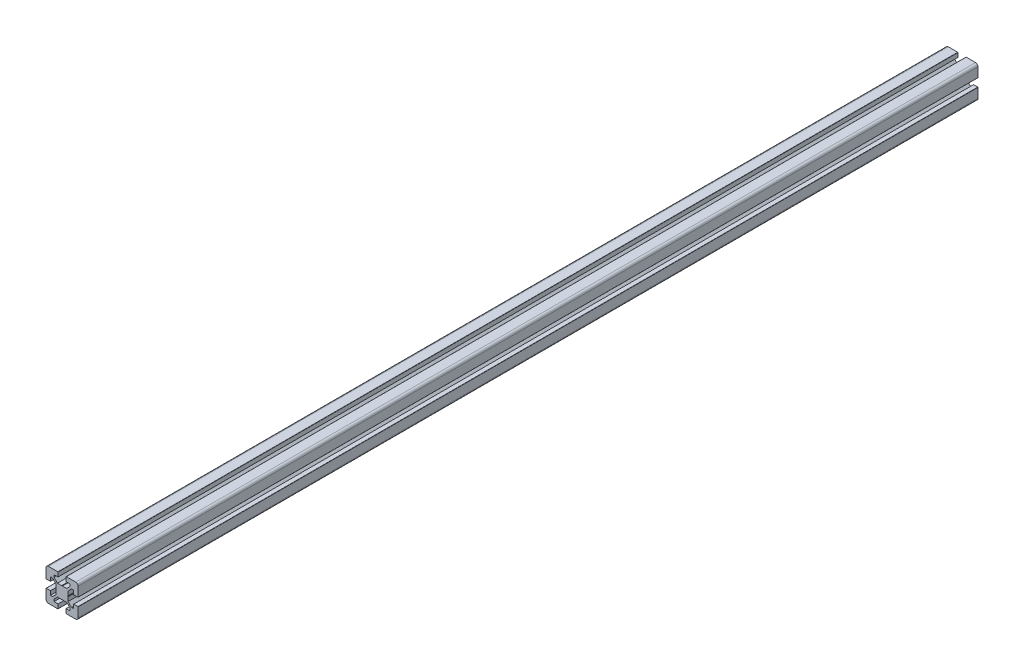
SolidWorks part; units mm, degrees
ref_plane "正面" through (0, 0, 0) normal (0, 0, 1) x (1, 0, 0)
ref_plane "平面" through (0, 0, 0) normal (0, 1, 0) x (1, 0, 0)
ref_plane "右側面" through (0, 0, 0) normal (1, 0, 0) x (0, 0, -1)
sketch "Model" plane through (0, 0, 0) normal (0, 0, 1) x (1, 0, 0)
  line L0 (160, 30) -> (160, 70)
  line L1 (110, 70) -> (110, 30)
  line L2 (160, 30) -> (110, 30)
  line L3 (110, 55) -> (160, 55)
  line L4 (110, 45) -> (160, 45)
  line L5 (160, 70) -> (110, 70)
  line L6 (105, 50) -> (165, 50) construction
  line L7 (110, 50.5196) -> (160, 50.5196)
  line L8 (110, 49.4804) -> (160, 49.4804)
  line L9 (110, 60) -> (160, 60) construction
  line L10 (110, 40) -> (160, 40) construction
  line L11 (37, 68) -> (33, 68)
  line L12 (69.7, 55) -> (64.5, 55)
  line L13 (64.5, 60) -> (64.5, 55)
  line L14 (70, 67) -> (70, 55.3)
  line L15 (68, 67) -> (68, 63)
  line L16 (64.5, 40) -> (64.5, 45)
  line L17 (69.7, 45) -> (64.5, 45)
  line L18 (70, 33) -> (70, 44.7)
  line L19 (68, 33) -> (68, 37)
  line L20 (33, 70) -> (44.7, 70)
  line L21 (60, 64.5) -> (60, 61.7678)
  line L22 (60, 64.5) -> (55, 64.5)
  line L23 (60, 61.7678) -> (55.7322, 57.5)
  line L24 (61.7678, 60) -> (57.5, 55.7322)
  line L25 (40, 64.5) -> (40, 61.7678)
  line L26 (40, 64.5) -> (45, 64.5)
  line L27 (40, 61.7678) -> (44.2678, 57.5)
  line L28 (35.5, 60) -> (38.2322, 60)
  line L29 (30.3, 55) -> (35.5, 55)
  line L30 (38.2322, 60) -> (42.5, 55.7322)
  line L31 (35.5, 55) -> (35.5, 60)
  line L32 (30, 67) -> (30, 55.3)
  line L33 (32, 67) -> (32, 63)
  line L34 (38, 67) -> (38, 63)
  line L35 (45, 69.7) -> (45, 64.5)
  line L36 (55, 69.7) -> (55, 64.5)
  line L37 (62, 67) -> (62, 63)
  line L38 (61.7678, 40) -> (57.5, 44.2678)
  line L39 (60, 35.5) -> (60, 38.2322)
  line L40 (60, 38.2322) -> (55.7322, 42.5)
  line L41 (55, 30.3) -> (55, 35.5)
  line L42 (62, 33) -> (62, 37)
  line L43 (38.2322, 40) -> (42.5, 44.2678)
  line L44 (40, 35.5) -> (40, 38.2322)
  line L45 (40, 35.5) -> (45, 35.5)
  line L46 (44.2678, 42.5) -> (49.4804, 42.5)
  line L47 (40, 38.2322) -> (44.2678, 42.5)
  line L48 (35.5, 45) -> (35.5, 40)
  line L49 (30.3, 45) -> (35.5, 45)
  line L50 (33, 38) -> (37, 38)
  line L51 (35.5, 40) -> (38.2322, 40)
  line L52 (33, 32) -> (37, 32)
  line L53 (33, 30) -> (44.7, 30)
  line L54 (30, 33) -> (30, 44.7)
  line L55 (32, 33) -> (32, 37)
  line L56 (38, 33) -> (38, 37)
  line L57 (45, 30.3) -> (45, 35.5)
  line L58 (50, 75) -> (50, 25) construction
  line L59 (57.5, 55.7322) -> (57.5, 50.5196)
  line L60 (67, 38) -> (63, 38)
  line L61 (25, 50) -> (75, 50) construction
  line L62 (64.5, 40) -> (61.7678, 40)
  line L63 (67, 62) -> (63, 62)
  line L64 (64.5, 60) -> (61.7678, 60)
  line L65 (42.5, 44.2678) -> (42.5, 49.4804)
  line L66 (37, 62) -> (33, 62)
  line L67 (44.2678, 57.5) -> (49.4804, 57.5)
  line L68 (57.5, 49.4804) -> (57.5, 44.2678)
  line L69 (42.5, 50.5196) -> (42.5, 55.7322)
  line L70 (50.5196, 57.5) -> (55.7322, 57.5)
  line L71 (55.3, 70) -> (67, 70)
  line L72 (63, 68) -> (67, 68)
  line L73 (55.3, 30) -> (67, 30)
  line L74 (63, 32) -> (67, 32)
  line L75 (55, 35.5) -> (60, 35.5)
  line L76 (50.5196, 42.5) -> (55.7322, 42.5)
  line L77 (57.2, 50) -> (57.5, 50.5196)
  line L78 (57.2, 50) -> (57.5, 49.4804)
  line L79 (42.8, 50) -> (42.5, 50.5196)
  line L80 (42.8, 50) -> (42.5, 49.4804)
  line L81 (50, 57.2) -> (49.4804, 57.5)
  line L82 (50, 57.2) -> (50.5196, 57.5)
  line L83 (50, 42.8) -> (49.4804, 42.5)
  line L84 (50, 42.8) -> (50.5196, 42.5)
  arc A0 (69.7, 55) -> (70, 55.3) centre (69.7, 55.3) ccw
  arc A1 (68, 67) -> (67, 68) centre (67, 67) ccw
  arc A2 (70, 44.7) -> (69.7, 45) centre (69.7, 44.7) ccw
  arc A3 (68, 37) -> (67, 38) centre (67, 37) ccw
  arc A4 (62, 63) -> (63, 62) centre (63, 63) ccw
  arc A5 (30, 55.3) -> (30.3, 55) centre (30.3, 55.3) ccw
  arc A6 (37, 62) -> (38, 63) centre (37, 63) ccw
  arc A7 (38, 67) -> (37, 68) centre (37, 67) ccw
  arc A8 (62, 33) -> (63, 32) centre (63, 33) ccw
  arc A9 (30.3, 45) -> (30, 44.7) centre (30.3, 44.7) ccw
  arc A10 (38, 37) -> (37, 38) centre (37, 37) ccw
  arc A11 (32, 33) -> (33, 32) centre (33, 33) ccw
  arc A12 (37, 32) -> (38, 33) centre (37, 33) ccw
  arc A13 (33, 38) -> (32, 37) centre (33, 37) ccw
  arc A14 (63, 38) -> (62, 37) centre (63, 37) ccw
  arc A15 (67, 62) -> (68, 63) centre (67, 63) ccw
  arc A16 (30, 33) -> (33, 30) centre (33, 33) ccw
  arc A17 (44.7, 30) -> (45, 30.3) centre (44.7, 30.3) ccw
  arc A18 (32, 63) -> (33, 62) centre (33, 63) ccw
  arc A19 (33, 68) -> (32, 67) centre (33, 67) ccw
  arc A20 (45, 69.7) -> (44.7, 70) centre (44.7, 69.7) ccw
  arc A21 (33, 70) -> (30, 67) centre (33, 67) ccw
  arc A22 (63, 68) -> (62, 67) centre (63, 67) ccw
  arc A23 (67, 32) -> (68, 33) centre (67, 33) ccw
  arc A24 (55, 30.3) -> (55.3, 30) centre (55.3, 30.3) ccw
  arc A25 (55.3, 70) -> (55, 69.7) centre (55.3, 69.7) ccw
  arc A26 (67, 30) -> (70, 33) centre (67, 33) ccw
  arc A27 (70, 67) -> (67, 70) centre (67, 67) ccw
  arc A28 (45.694, 53.0035) -> (45.694, 46.9966) centre (50, 50) ccw
  arc A29 (46.9981, 45.6929) -> (53.0039, 45.6943) centre (50, 50) ccw
  arc A30 (54.3061, 46.9967) -> (54.3061, 53.0034) centre (50, 50) ccw
  arc A31 (53.0033, 54.3061) -> (46.9968, 54.3062) centre (50, 50) ccw
  arc A32 (46.4038, 54.6058) -> (45.3944, 53.5962) centre (45.4038, 54.5962) ccw
  arc A33 (54.608, 53.5963) -> (53.5962, 54.6065) centre (54.5962, 54.5962) ccw
  arc A34 (53.5962, 45.3942) -> (54.6061, 46.4038) centre (54.5962, 45.4038) ccw
  arc A35 (45.3939, 46.4037) -> (46.4038, 45.3942) centre (45.4038, 45.4038) ccw
  arc A36 (45.694, 53.0035) -> (45.3944, 53.5962) centre (45.3778, 53.2158) ccw
  arc A37 (46.4038, 54.6058) -> (46.9968, 54.3062) centre (46.7842, 54.6222) ccw
  arc A38 (54.608, 53.5963) -> (54.3061, 53.0034) centre (54.6221, 53.2158) ccw
  arc A39 (53.0033, 54.3061) -> (53.5962, 54.6065) centre (53.2158, 54.6221) ccw
  arc A40 (45.3939, 46.4037) -> (45.694, 46.9966) centre (45.3778, 46.7842) ccw
  arc A41 (46.9981, 45.6929) -> (46.4038, 45.3942) centre (46.7842, 45.3779) ccw
  arc A42 (54.3061, 46.9967) -> (54.6061, 46.4038) centre (54.6222, 46.7842) ccw
  arc A43 (53.5962, 45.3942) -> (53.0039, 45.6943) centre (53.2158, 45.3778) ccw
  text T0 "HFS84040" font "SWTXT" height 4
  text T1 "HFS8-4040-50" font "SWTXT" height 4
extrude "ﾎﾞｽ - 押し出し1" add sketch "Model" against normal blind 1120 contours L20 A20 L35 L26 L25 L27 L67 L81 L82 L70 L23 L21 L22 L36 A25 L71 A27 L14 A0 L12 L13 L64 L24 L59 L77 L78 L68 L38 L62 L16 L17 A2 L18 A26 L73 A24 L41 L75 L39 L40 L76 L84 L83 L46 L47 L44 L45 L57 A17 L53 A16 L54 A9 L49 L48 L51 L43 L65 L80 L79 L69 L30 L28 L31 L29 A5 L32 A21
